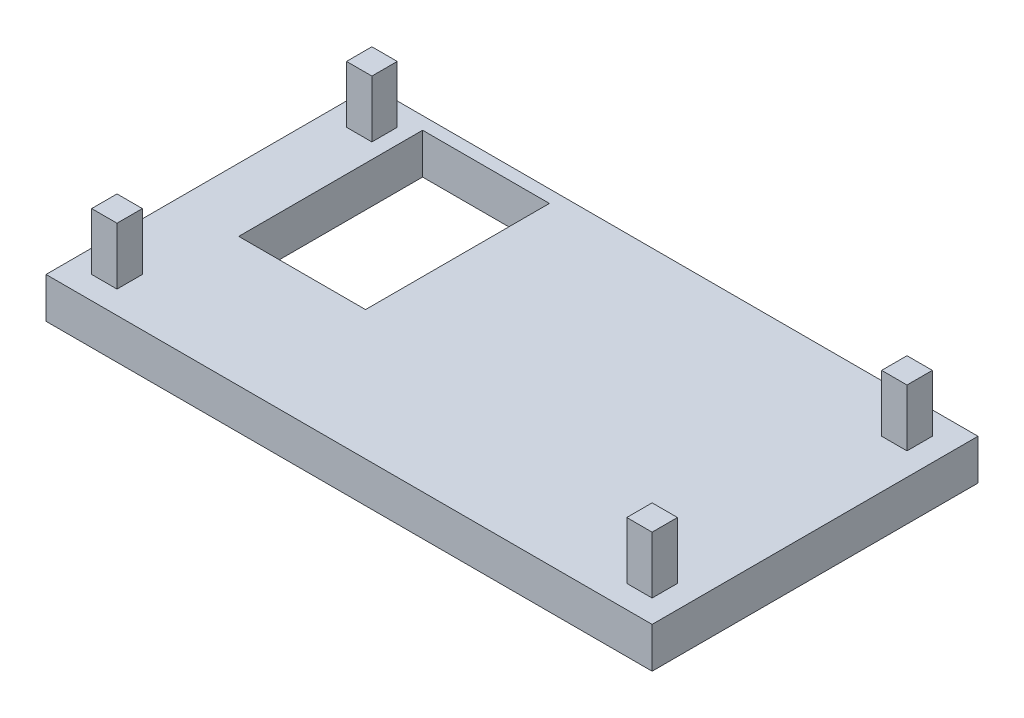
SolidWorks part; units mm, degrees
ref_plane "Piano frontale" through (0, 0, 0) normal (0, 0, 1) x (1, 0, 0)
ref_plane "Piano superiore" through (0, 0, 0) normal (0, 1, 0) x (1, 0, 0)
ref_plane "Piano destro" through (0, 0, 0) normal (1, 0, 0) x (0, 0, -1)
sketch "Schizzo1" plane through (0, 0, 0) normal (0, 1, 0) x (1, 0, 0)
  line L1 (-23.9, -12.85) -> (23.9, -12.85)
  line L2 (-23.9, -12.85) -> (-23.9, 12.85)
  line L3 (-23.9, 12.85) -> (23.9, 12.85)
  line L4 (23.9, -12.85) -> (23.9, 12.85)
  line L5 (-23.9, -12.85) -> (23.9, 12.85) construction
  line L6 (-23.9, 12.85) -> (23.9, -12.85) construction
  point P0 (0, 0)
  dimension "D1" = 25.7
  dimension "D2" = 47.8
extrude "Estrusione-Estrusione2" add sketch "Schizzo1" along normal blind 3.2
sketch "Schizzo3" plane through (0, 3.2, 0) normal (0, 1, 0) x (1, 0, 0)
  line L0 (23.9, -12.85) -> (23.9, 12.85) construction
  line L1 (22.1, -11.05) -> (20.1, -11.05)
  line L2 (22.1, -11.05) -> (22.1, -9.05)
  line L3 (22.1, -9.05) -> (20.1, -9.05)
  line L4 (20.1, -11.05) -> (20.1, -9.05)
  line L5 (22.1, -11.05) -> (20.1, -9.05) construction
  line L6 (22.1, -9.05) -> (20.1, -11.05) construction
  line L7 (-23.9, -12.85) -> (23.9, -12.85) construction
  line L8 (0, -12.85) -> (0, 8.453) construction
  line L9 (23.9, 0) -> (-7.4415, 0) construction
  line L10 (22.1, 9.05) -> (20.1, 11.05) construction
  line L11 (22.1, 11.05) -> (20.1, 9.05) construction
  line L12 (20.1, 11.05) -> (20.1, 9.05)
  line L13 (22.1, 9.05) -> (20.1, 9.05)
  line L14 (22.1, 11.05) -> (22.1, 9.05)
  line L15 (22.1, 11.05) -> (20.1, 11.05)
  line L16 (-22.1, 11.05) -> (-20.1, 9.05) construction
  line L17 (-22.1, 9.05) -> (-20.1, 11.05) construction
  line L18 (-22.1, -9.05) -> (-20.1, -11.05) construction
  line L19 (-22.1, -11.05) -> (-20.1, -9.05) construction
  line L20 (-22.1, 11.05) -> (-20.1, 11.05)
  line L21 (-22.1, 11.05) -> (-22.1, 9.05)
  line L22 (-22.1, 9.05) -> (-20.1, 9.05)
  line L23 (-20.1, 11.05) -> (-20.1, 9.05)
  line L24 (-20.1, -11.05) -> (-20.1, -9.05)
  line L25 (-22.1, -9.05) -> (-20.1, -9.05)
  line L26 (-22.1, -11.05) -> (-22.1, -9.05)
  line L27 (-22.1, -11.05) -> (-20.1, -11.05)
  point P0 (21.1, -10.05)
  point P18 (21.1, 10.05)
  point P27 (-21.1, 10.05)
  point P28 (-21.1, -10.05)
  dimension "D1" = 2
  dimension "D2" = 2
  dimension "D3" = 1.8
  dimension "D4" = 1.8
extrude "Estrusione-Estrusione4" add sketch "Schizzo3" along normal blind 4.5
sketch "Schizzo4" plane through (0, 0, 0) normal (0, -1, 0) x (1, 0, 0)
  line L0 (-23.9, -12.85) -> (-23.9, 12.85) construction
  line L1 (-18.9, 2.65) -> (-8.9, 2.65)
  line L2 (-18.9, 2.65) -> (-18.9, -11.85)
  line L3 (-18.9, -11.85) -> (-8.9, -11.85)
  line L4 (-8.9, 2.65) -> (-8.9, -11.85)
  line L5 (-18.9, 2.65) -> (-8.9, -11.85) construction
  line L6 (-18.9, -11.85) -> (-8.9, 2.65) construction
  line L8 (23.9, -12.85) -> (-23.9, -12.85) construction
  point P0 (-13.9, -4.6)
  dimension "D1" = 10
  dimension "D2" = 14.5
  dimension "D3" = 5
  dimension "D4" = 1
extrude "Taglio-Estrusione1" cut sketch "Schizzo4" against normal blind 5
